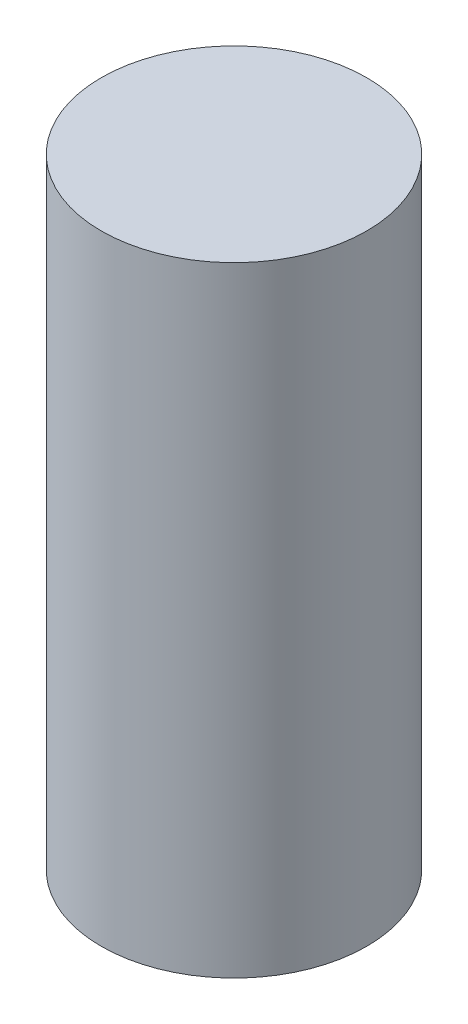
SolidWorks part; units mm, degrees
ref_plane "Front Plane" through (0, 0, 0) normal (0, 0, 1) x (1, 0, 0)
ref_plane "Top Plane" through (0, 0, 0) normal (0, 1, 0) x (1, 0, 0)
ref_plane "Right Plane" through (0, 0, 0) normal (1, 0, 0) x (0, 0, -1)
sketch "Sketch1" plane through (0, 0, 0) normal (0, 0, 1) x (1, 0, 0)
  line L0 (0, 0) -> (0.762, 0)
  line L1 (0.762, 0) -> (0.762, 8.89)
  line L2 (0.762, 8.89) -> (-1.143, 8.89)
  line L3 (-1.143, 8.89) -> (-1.143, 5.08)
  line L4 (-1.143, 5.08) -> (0, 5.08)
  line L5 (0, 5.08) -> (0, 0)
  line L6 (-1.143, 0.1505) -> (-1.143, 10.636) construction
  dimension "D1" = 1.905
  dimension "D2" = 1.143
  dimension "D3" = 8.89
  dimension "D4" = 5.08
revolve "Revolve1" add sketch "Sketch1" angle 360 about L6
